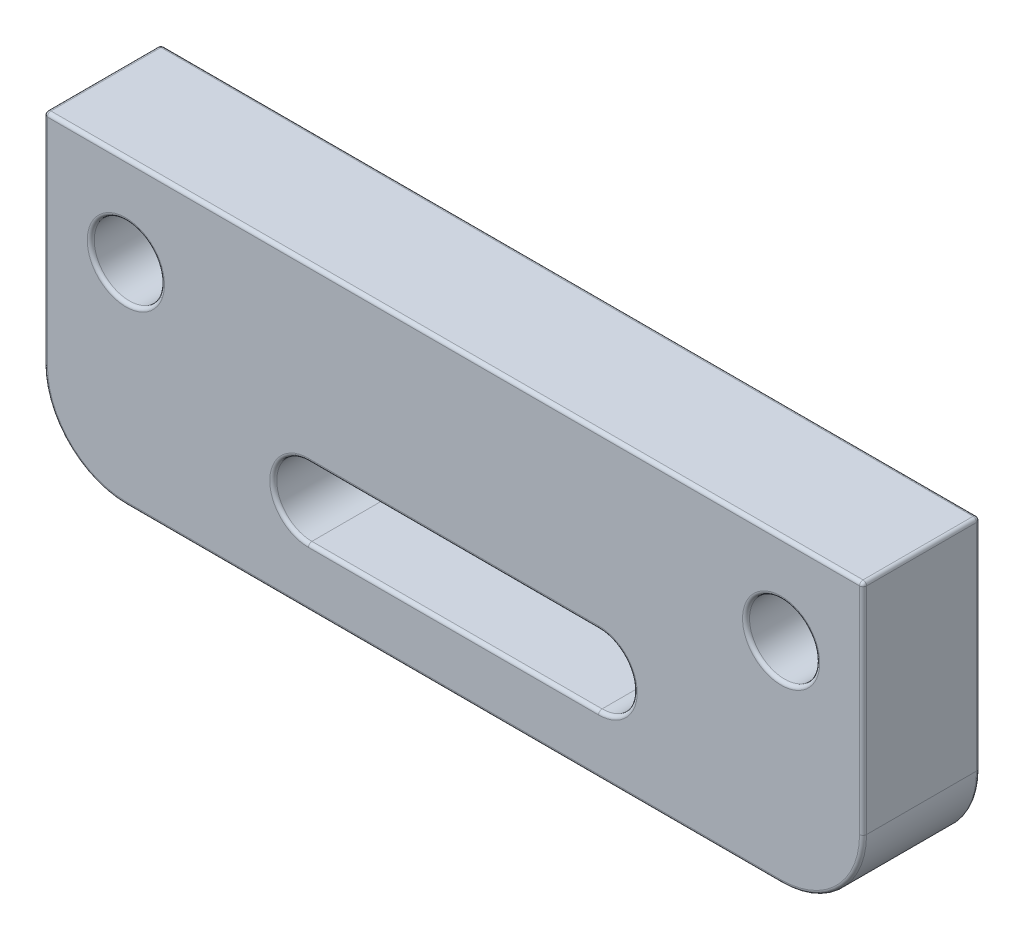
SolidWorks part; units mm, degrees
ref_plane "Front Plane" through (0, 0, 0) normal (0, 0, 1) x (1, 0, 0)
ref_plane "Top Plane" through (0, 0, 0) normal (0, 1, 0) x (1, 0, 0)
ref_plane "Right Plane" through (0, 0, 0) normal (1, 0, 0) x (0, 0, -1)
sketch "Sketch1" plane through (0, 0, 0) normal (0, 0, 1) x (1, 0, 0)
  line L0 (0, 26) -> (0, -19) construction
  line L5 (-11.5, 6) -> (11.5, 6)
  line L6 (-11.5, 6) -> (-11.5, -6)
  line L7 (-11.5, -6) -> (11.5, -6)
  line L8 (11.5, 6) -> (11.5, -6)
  line L9 (-11.5, 6) -> (11.5, -6) construction
  line L10 (-11.5, -6) -> (11.5, 6) construction
  line L11 (-6.2, -15) -> (6.2, -15) construction
  line L12 (-6.2, -13.5) -> (6.2, -13.5)
  line L13 (-6.2, -16.5) -> (6.2, -16.5)
  line L15 (-17.5, 9) -> (17.5, 9)
  line L16 (-17.5, 9) -> (-17.5, -19)
  line L17 (-17.5, -19) -> (17.5, -19)
  line L18 (17.5, 9) -> (17.5, -19)
  arc A0 (-6.2, -13.5) -> (-6.2, -16.5) centre (-6.2, -15) ccw
  arc A1 (6.2, -16.5) -> (6.2, -13.5) centre (6.2, -15) ccw
  circle A2 centre (-14, -10) radius 1.5
  circle A3 centre (-14, 0) radius 1
  circle A4 centre (-8.5, 16) radius 2
  circle A5 centre (14, -10) radius 1.5
  circle A6 centre (14, 0) radius 1
  circle A7 centre (8.5, 16) radius 2
  arc A8 (-17.5, 9) -> (17.5, 9) centre (0, 8.4926) cw
  point P0 (0, 0)
  point P10 (0, -15)
  point P19 (0, -19)
  point P26 (0, 26)
  dimension "D5" = 1.5
  dimension "D10" = 2
  dimension "D13" = 3
  dimension "D14" = 4
  dimension "D16" = 8.5
  dimension "D1" = 23
  dimension "D2" = 12
  dimension "D3" = 45
  dimension "D4" = 13
  dimension "D6" = 12.4
  dimension "D7" = 4
  dimension "D8" = 28
  dimension "D9" = 35
  dimension "D11" = 2.5
  dimension "D12" = 10
  dimension "D15" = 10
extrude "Boss-Extrude1" add sketch "Sketch1" along normal blind 5 contours A8 L15 A4 A7 | L18 L15 L16 L17 A5 A3 A2 A1 L13 A0 L12 L5 L8 L7 L6 A6
fillet "Fillet1" radius 3.5 2 edges at (-17.5, -19, 2.5) (17.5, -19, 2.5)
fillet "Fillet2" radius 0.15 40 edges at (15, 0, 5) (15, 0, 0) (11.5, 0, 0) (11.5, 0, 5) (0, -6, 0) (0, -6, 5) (-11.5, 0, 0) (-11.5, 0, 5) (0, 6, 0) (0, 6, 5) (0, -16.5, 0) (0, -16.5, 5) (-7.7, -15, 0) (-7.7, -15, 5) (0, -13.5, 0) (0, -13.5, 5) (7.7, -15, 0) (7.7, -15, 5) (-12.5, -10, 5) (-12.5, -10, 0) (-13, 0, 5) (-13, 0, 0) (15.5, -10, 5) (15.5, -10, 0) (10.5, 16, 5) (10.5, 16, 0) (-6.5, 16, 5) (-6.5, 16, 0) (16.4749, -17.9749, 5) (16.4749, -17.9749, 0) (17.5, -3.25, 5) (17.5, -3.25, 0) (0, 26, 0) (0, 26, 5) (-17.5, -3.25, 0) (-17.5, -3.25, 5) (-16.4749, -17.9749, 5) (-16.4749, -17.9749, 0) (0, -19, 5) (0, -19, 0)
sketch "Sketch2" plane through (0, 0, 5) normal (0, 0, 1) x (1, 0, 0)
  line L0 (-22.35, -6.15) -> (27.65, -6.15)
  line L1 (11.65, -6.15) -> (-11.65, -6.15) construction
  line L2 (-17.35, 8.9978) -> (-17.35, -15.5) construction
  dimension "D1" = 50
  dimension "D2" = 5
extrude "Cut-Extrude1" cut sketch "Sketch2" against normal through all both and the other way through all
fillet "Fillet3" radius 0.15 8 edges at (17.4561, -6.15, 4.9561) (17.5, -6.15, 2.5) (17.4561, -6.15, 0.0439) (0, -6.15, 0) (-17.4561, -6.15, 0.0439) (-17.5, -6.15, 2.5) (-17.4561, -6.15, 4.9561) (0, -6.15, 5)
